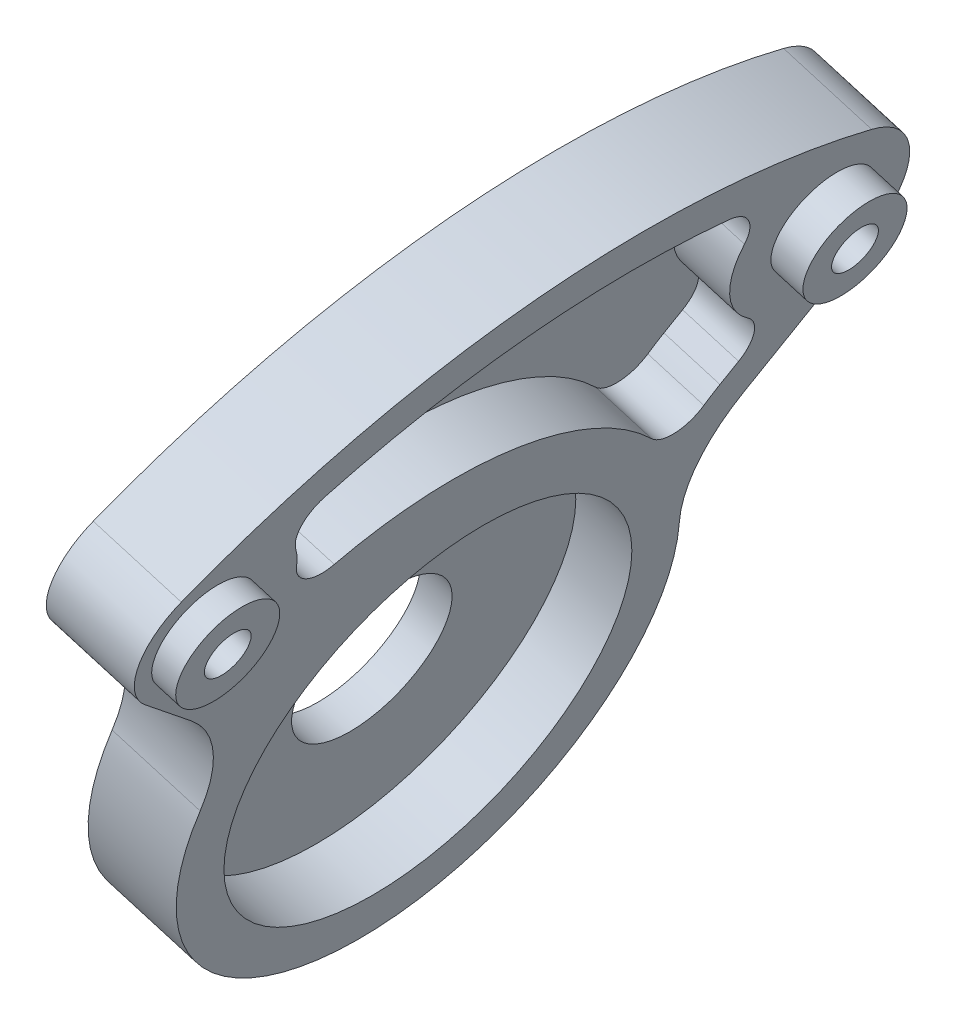
SolidWorks part; units mm, degrees
ref_plane "Front Plane" through (0, 0, 0) normal (0, 0, 1) x (1, 0, 0)
ref_plane "Top Plane" through (0, 0, 0) normal (0, 1, 0) x (1, 0, 0)
ref_plane "Right Plane" through (0, 0, 0) normal (1, 0, 0) x (0, 0, -1)
ref_plane "Plane1" through (65.3568, -19.3231, 0) normal (-0.959, 0.2835, 0) x (-0.2835, -0.959, 0)
sketch "Sketch1" plane through (65.3568, -19.3231, 0) normal (-0.959, 0.2835, 0) x (-0.2835, -0.959, 0)
  line L0 (-22.4092, 105.5353) -> (-25.7082, 109.2487)
  line L1 (-29.6225, 66.9796) -> (-23.1666, 72.7151)
  arc A0 (-23.1666, 72.7151) -> (-16.0418, 74.5266) centre (-17.8533, 66.7344) cw
  arc A1 (-16.0418, 74.5266) -> (-15.1237, 102.9558) centre (-12.7586, 88.65) ccw
  arc A2 (-15.1237, 102.9558) -> (-22.4092, 105.5353) centre (-16.4286, 110.8487) cw
  arc A3 (-25.7082, 109.2487) -> (-31.9893, 108.866) centre (-28.6986, 106.592) ccw
  arc A4 (-31.9893, 108.866) -> (-37.6902, 69.1467) centre (5.0315, 83.2837) ccw
  arc A5 (-37.6902, 69.1467) -> (-29.6225, 66.9796) centre (-32.9433, 70.7175) ccw
extrude "Boss-Extrude1" add sketch "Sketch1" against normal blind 5.5
sketch "Sketch2" plane through (70.6311, -20.8825, 0) normal (0.959, -0.2835, 0) x (0, 0, -1)
  circle A0 centre (-106.592, 28.6986) radius 3
extrude "Boss-Extrude2" add sketch "Sketch2" along normal blind 1.5
sketch "Sketch3" plane through (65.3568, -19.3231, 0) normal (-0.959, 0.2835, 0) x (0, 0, 1)
  circle A0 centre (106.592, 28.6986) radius 1.35
extrude "Cut-Extrude1" cut sketch "Sketch3" against normal through all
sketch "Sketch4" plane through (70.6311, -20.8825, 0) normal (0.959, -0.2835, 0) x (0, 0, -1)
  circle A0 centre (-70.7175, 32.9433) radius 3
extrude "Boss-Extrude3" add sketch "Sketch4" along normal blind 2
sketch "Sketch5" plane through (65.3568, -19.3231, 0) normal (-0.959, 0.2835, 0) x (0, 0, 1)
  circle A0 centre (70.7175, 32.9433) radius 1.35
extrude "Cut-Extrude2" cut sketch "Sketch5" against normal through all
sketch "Sketch6" plane through (70.6311, -20.8825, 0) normal (0.959, -0.2835, 0) x (0, 0, -1)
  circle A0 centre (-88.65, 12.7586) radius 11.75
extrude "Cut-Extrude3" cut sketch "Sketch6" against normal blind 3.5
sketch "Sketch7" plane through (65.3568, -19.3231, 0) normal (-0.959, 0.2835, 0) x (0, 0, 1)
  circle A0 centre (88.65, 12.7586) radius 4.625
extrude "Cut-Extrude4" cut sketch "Sketch7" against normal through all
sketch "Sketch8" plane through (70.6311, -20.8825, 0) normal (0.959, -0.2835, 0) x (0, 0, -1)
  line L0 (-74.584, 24.827) -> (-73.7366, 25.7809)
  arc A0 (-73.7366, 25.7809) -> (-74.0078, 28.691) centre (-75.2317, 27.1093) ccw
  arc A1 (-74.0078, 28.691) -> (-75.861, 34.5094) centre (-70.7175, 32.9433) cw
  arc A2 (-75.861, 34.5094) -> (-77.5022, 37.0734) centre (-77.7743, 35.092) ccw
  arc A3 (-77.5022, 37.0734) -> (-100.7617, 33.7082) centre (-83.2837, -5.0315) ccw
  arc A4 (-100.7617, 33.7082) -> (-101.7429, 31.0212) centre (-99.9392, 31.8852) ccw
  arc A5 (-101.7429, 31.0212) -> (-101.2964, 29.6286) centre (-106.592, 28.6986) cw
  arc A6 (-101.2964, 29.6286) -> (-98.6065, 28.1087) centre (-99.3266, 29.9746) ccw
  arc A7 (-98.6065, 28.1087) -> (-78.3556, 23.6958) centre (-91.8278, 10.5438) cw
  arc A8 (-78.3556, 23.6958) -> (-75.294, 23.9346) centre (-76.9245, 25.0929) ccw
  arc A9 (-75.294, 23.9346) -> (-74.584, 24.827) centre (-66.7344, 17.8533) cw
extrude "Cut-Extrude5" cut sketch "Sketch8" against normal blind 3.5
sketch "Sketch9" plane through (67.2747, -19.8902, 0) normal (0.959, -0.2835, 0) x (0, 0, -1)
  line L0 (-88.65, 19.7586) -> (-88.65, 12.7586) construction
  circle A0 centre (-88.65, 19.7586) radius 1.35
  circle A1 centre (-88.65, 12.7586) radius 4.625 construction
  circle A2 centre (-81.65, 12.7586) radius 1.35
  circle A3 centre (-88.65, 5.7586) radius 1.35
  circle A4 centre (-95.65, 12.7586) radius 1.35
  point P8 (-88.65, 12.7586)
  point P17 (-88.65, 12.7586)
  dimension "D1" = 2.7
  dimension "D2" = 7
  dimension "D3" = 4
